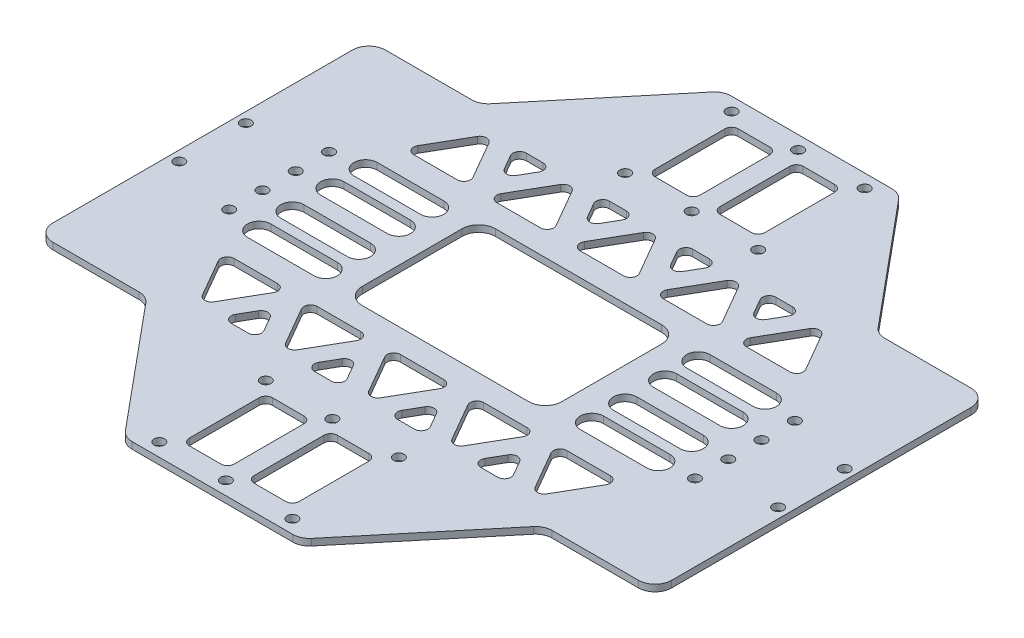
SolidWorks part; units mm, degrees
material "Hexcel AS4C (3000 丝)"
ref_plane "前视基准面" through (0, 0, 0) normal (0, 0, 1) x (1, 0, 0)
ref_plane "上视基准面" through (0, 0, 0) normal (0, 1, 0) x (1, 0, 0)
ref_plane "右视基准面" through (0, 0, 0) normal (1, 0, 0) x (0, 0, -1)
sketch "草图1" plane through (0, 0, 0) normal (0, 1, 0) x (1, 0, 0)
  line L0 (-90, 50) -> (-90, -50) construction
  line L1 (-93, 50) -> (93, 50)
  line L2 (-93, 50) -> (-93, -50)
  line L3 (-93, -50) -> (93, -50)
  line L4 (93, 50) -> (93, -50)
  line L5 (0, -50) -> (0, 50) construction
  line L6 (-93, 0) -> (93, 0) construction
  circle A0 centre (-90, 10) radius 1.6
  circle A1 centre (-90, -10) radius 1.6
  circle A2 centre (90, -10) radius 1.6
  circle A3 centre (90, 10) radius 1.6
  point P0 (0, 0)
  dimension "D3" = 3.2
  dimension "D1" = 100
  dimension "187" = 186
  dimension "D2" = 3
  dimension "D4" = 10
extrude "凸台-拉伸1" add sketch "草图1" along normal blind 2
sketch "草图2" plane through (0, 0, 0) normal (0, -1, 0) x (1, 0, 0)
  line L0 (0, 50) -> (0, -49950) construction
  line L1 (-93, 50) -> (93, 50) construction
  line L2 (-93.5, 0) -> (49906.5, 0) construction
  line L3 (-26.5, 50) -> (26.5, 50)
  line L4 (-26.5, 50) -> (-26.5, 90)
  line L5 (-26.5, 90) -> (26.5, 90)
  line L6 (26.5, 50) -> (26.5, 90)
  line L7 (0, 90) -> (0, 50) construction
  line L8 (-26.5, 70) -> (26.5, 70) construction
  line L9 (-93, -50) -> (-93, 50) construction
  line L10 (-26.5, -90) -> (26.5, -90)
  line L11 (26.5, -50) -> (26.5, -90)
  line L12 (-26.5, -50) -> (26.5, -50)
  line L13 (-26.5, -50) -> (-26.5, -90)
  line L14 (-20, 54) -> (20, 54) construction
  line L15 (-20, 86) -> (20, 86) construction
  line L16 (-20, 86) -> (-20, 54) construction
  line L17 (-20, 54) -> (20, 54) construction
  line L18 (20, 86) -> (20, 54) construction
  line L19 (0, 54) -> (0, 86) construction
  line L20 (-20, 70) -> (20, 70) construction
  line L21 (-20, -70) -> (20, -70) construction
  line L22 (0, -54) -> (0, -86) construction
  line L23 (20, -86) -> (20, -54) construction
  line L24 (-20, -54) -> (20, -54) construction
  line L25 (-20, -86) -> (-20, -54) construction
  line L26 (-20, -86) -> (20, -86) construction
  line L27 (-20, -54) -> (20, -54) construction
  line L28 (-26.5, -70) -> (26.5, -70) construction
  circle A0 centre (-20, 86) radius 1.6
  circle A1 centre (0, 86) radius 1.6
  circle A2 centre (20, 86) radius 1.6
  circle A3 centre (20, 54) radius 1.6
  circle A4 centre (0, 54) radius 1.6
  circle A5 centre (-20, 54) radius 1.6
  circle A6 centre (-20, -54) radius 1.6
  circle A7 centre (0, -54) radius 1.6
  circle A8 centre (20, -54) radius 1.6
  circle A9 centre (20, -86) radius 1.6
  circle A10 centre (0, -86) radius 1.6
  circle A11 centre (-20, -86) radius 1.6
  point P4 (0, 50)
  point P13 (-93, 0)
  point P18 (0, 70)
  point P44 (0, -70)
  point P81 (0, 70)
  dimension "D4" = 3.2
  dimension "D1" = 40
  dimension "D2" = 32
  dimension "50" = 53
  dimension "D3" = 40
extrude "凸台-拉伸2" add sketch "草图2" against normal up to surface (2 mm away) up to face at (90, 2, 8.4)
sketch "草图3" plane through (0, 2, 0) normal (0, 1, 0) x (1, 0, 0)
  line L0 (0, 90) -> (0, -49910) construction
  line L1 (-26.5, 90) -> (26.5, 90) construction
  line L2 (-93.5, 0) -> (49906.5, 0) construction
  line L3 (-93, 50) -> (-93, -50) construction
  line L4 (-70, 50) -> (-70, -50) construction
  line L5 (-26.5, 50) -> (-93, 50) construction
  line L6 (-93, -50) -> (-26.5, -50) construction
  line L7 (-70, -15) -> (-70, -5) construction
  line L8 (70, -15) -> (70, -5) construction
  circle A0 centre (-70, -15) radius 1.6
  circle A1 centre (-70, -5) radius 1.6
  circle A2 centre (-70, 5) radius 1.6
  circle A3 centre (-70, 15) radius 1.6
  circle A4 centre (70, 15) radius 1.6
  circle A5 centre (70, 5) radius 1.6
  circle A6 centre (70, -5) radius 1.6
  circle A7 centre (70, -15) radius 1.6
  point P4 (0, 90)
  point P9 (-93, 0)
  dimension "D1" = 3.2
  dimension "D3" = 10
  dimension "D4" = 15
  dimension "D5" = 70
  dimension "D2" = 4
extrude "切除-拉伸1" cut sketch "草图3" against normal through all
sketch "草图4" plane through (0, 2, 0) normal (0, 1, 0) x (1, 0, 0)
  line L0 (-26.5, 90) -> (-59.75, 50)
  line L1 (-26.5, 50) -> (-93, 50) construction
  line L2 (-59.75, 50) -> (-26.5, 50)
  line L3 (-26.5, 50) -> (-26.5, 90)
  line L4 (0, 90) -> (0, -49910) construction
  line L5 (-26.5, 90) -> (26.5, 90) construction
  line L6 (-93.5, 0) -> (-50093.5, 0) construction
  line L7 (-93, 50) -> (-93, -50) construction
  line L8 (59.75, 50) -> (26.5, 50)
  line L9 (26.5, 90) -> (59.75, 50)
  line L10 (26.5, 50) -> (26.5, 90)
  line L11 (26.5, -90) -> (59.75, -50)
  line L12 (26.5, -50) -> (26.5, -90)
  line L13 (59.75, -50) -> (26.5, -50)
  line L14 (-59.75, -50) -> (-26.5, -50)
  line L15 (-26.5, -90) -> (-59.75, -50)
  line L16 (-26.5, -50) -> (-26.5, -90)
  point P11 (0, 90)
  point P16 (-93, 0)
extrude "凸台-拉伸3" add sketch "草图4" against normal up to surface (2 mm away) up to face at (-70, 0, 6.6)
sketch "草图5" plane through (0, 0, 0) normal (0, -1, 0) x (1, 0, 0)
  line L0 (-93.5, 0) -> (-50093.5, 0) construction
  line L1 (-93, -50) -> (-93, 50) construction
  line L2 (16.5, 57.5) -> (3, 57.5)
  line L3 (-16.5, 82.5) -> (-3, 82.5)
  line L4 (-20, 86) -> (20, 86) construction
  line L5 (-20, 86) -> (-20, 54) construction
  line L6 (-20, 54) -> (20, 54) construction
  line L7 (20, 86) -> (20, 54) construction
  line L8 (0, 54) -> (0, 86) construction
  line L9 (-20, 70) -> (20, 70) construction
  line L10 (-16.5, 82.5) -> (-16.5, 57.5)
  line L11 (-16.5, 57.5) -> (-3, 57.5)
  line L12 (-3, 82.5) -> (-3, 57.5)
  line L13 (-9.75, 57.5) -> (-9.75, 82.5) construction
  line L14 (-16.5, 70) -> (-3, 70) construction
  line L15 (3, 82.5) -> (3, 57.5)
  line L16 (16.5, 82.5) -> (3, 82.5)
  line L17 (16.5, 82.5) -> (16.5, 57.5)
  line L18 (16.5, -82.5) -> (16.5, -57.5)
  line L19 (16.5, -82.5) -> (3, -82.5)
  line L20 (3, -82.5) -> (3, -57.5)
  line L21 (16.5, -57.5) -> (3, -57.5)
  line L22 (-16.5, -57.5) -> (-3, -57.5)
  line L23 (-3, -82.5) -> (-3, -57.5)
  line L24 (-16.5, -82.5) -> (-3, -82.5)
  line L25 (-16.5, -82.5) -> (-16.5, -57.5)
  line L26 (-60, -6) -> (-40, -6) construction
  line L27 (-60, -2.5) -> (-40, -2.5)
  line L28 (-30, 20) -> (30, 20)
  line L29 (-30, 20) -> (-30, -20)
  line L30 (-30, -20) -> (30, -20)
  line L31 (30, 20) -> (30, -20)
  line L32 (0, -20) -> (0, 20) construction
  line L33 (-30, 0) -> (30, 0) construction
  line L34 (-60, -9.5) -> (-40, -9.5)
  line L35 (-70, -5) -> (-30, -5) construction
  line L36 (-50, -5) -> (-50, -50005) construction
  line L37 (-60, -19.5) -> (-40, -19.5)
  line L38 (-60, -12.5) -> (-40, -12.5)
  line L39 (-60, -16) -> (-40, -16) construction
  line L40 (-60, -9.5) -> (-60, -19.5) construction
  line L41 (-60, 16) -> (-40, 16) construction
  line L42 (-60, 12.5) -> (-40, 12.5)
  line L43 (-60, 19.5) -> (-40, 19.5)
  line L44 (-60, 6) -> (-40, 6) construction
  line L45 (-60, 2.5) -> (-40, 2.5)
  line L46 (-60, 9.5) -> (-40, 9.5)
  line L47 (60, 6) -> (40, 6) construction
  line L48 (60, 2.5) -> (40, 2.5)
  line L49 (60, 9.5) -> (40, 9.5)
  line L50 (60, 16) -> (40, 16) construction
  line L51 (60, 12.5) -> (40, 12.5)
  line L52 (60, 19.5) -> (40, 19.5)
  line L53 (60, -16) -> (40, -16) construction
  line L54 (60, -12.5) -> (40, -12.5)
  line L55 (60, -19.5) -> (40, -19.5)
  line L56 (60, -6) -> (40, -6) construction
  line L57 (60, -2.5) -> (40, -2.5)
  line L58 (60, -9.5) -> (40, -9.5)
  line L59 (0, 0) -> (0, -50000) construction
  line L60 (-50, 44.3205) -> (-60, 27)
  line L61 (-60, 27) -> (-40, 27)
  line L62 (-40, 27) -> (-50, 44.3205)
  line L63 (-15, 27) -> (-25, 44.3205)
  line L64 (-25, 44.3205) -> (-35, 27)
  line L65 (-35, 27) -> (-15, 27)
  line L66 (10, 27) -> (0, 44.3205)
  line L67 (0, 44.3205) -> (-10, 27)
  line L68 (-10, 27) -> (10, 27)
  line L69 (35, 27) -> (25, 44.3205)
  line L70 (25, 44.3205) -> (15, 27)
  line L71 (15, 27) -> (35, 27)
  line L72 (60, 27) -> (50, 44.3205)
  line L73 (50, 44.3205) -> (40, 27)
  line L74 (40, 27) -> (60, 27)
  line L75 (-40, 27) -> (-15, 27) construction
  line L76 (-43.5, 44.3205) -> (-31.5, 44.3205)
  line L77 (-31.5, 44.3205) -> (-37.5, 33.9282)
  line L78 (-37.5, 33.9282) -> (-43.5, 44.3205)
  line L79 (-50, 44.3205) -> (-25, 44.3205) construction
  line L80 (-37.5, 44.3205) -> (-37.5, -49955.6795) construction
  line L81 (-12.5, 33.9282) -> (-18.5, 44.3205)
  line L82 (-18.5, 44.3205) -> (-6.5, 44.3205)
  line L83 (-6.5, 44.3205) -> (-12.5, 33.9282)
  line L84 (12.5, 33.9282) -> (6.5, 44.3205)
  line L85 (6.5, 44.3205) -> (18.5, 44.3205)
  line L86 (18.5, 44.3205) -> (12.5, 33.9282)
  line L87 (37.5, 33.9282) -> (31.5, 44.3205)
  line L88 (31.5, 44.3205) -> (43.5, 44.3205)
  line L89 (43.5, 44.3205) -> (37.5, 33.9282)
  line L90 (-37.5, 33.9282) -> (-12.5, 33.9282) construction
  line L91 (-37.5, -33.9282) -> (-12.5, -33.9282) construction
  line L92 (-50, -44.3205) -> (-25, -44.3205) construction
  line L93 (-40, -27) -> (-15, -27) construction
  line L94 (43.5, -44.3205) -> (37.5, -33.9282)
  line L95 (31.5, -44.3205) -> (43.5, -44.3205)
  line L96 (37.5, -33.9282) -> (31.5, -44.3205)
  line L97 (18.5, -44.3205) -> (12.5, -33.9282)
  line L98 (6.5, -44.3205) -> (18.5, -44.3205)
  line L99 (12.5, -33.9282) -> (6.5, -44.3205)
  line L100 (-6.5, -44.3205) -> (-12.5, -33.9282)
  line L101 (-18.5, -44.3205) -> (-6.5, -44.3205)
  line L102 (-12.5, -33.9282) -> (-18.5, -44.3205)
  line L103 (-37.5, -33.9282) -> (-43.5, -44.3205)
  line L104 (-31.5, -44.3205) -> (-37.5, -33.9282)
  line L105 (-43.5, -44.3205) -> (-31.5, -44.3205)
  line L106 (40, -27) -> (60, -27)
  line L107 (50, -44.3205) -> (40, -27)
  line L108 (60, -27) -> (50, -44.3205)
  line L109 (15, -27) -> (35, -27)
  line L110 (25, -44.3205) -> (15, -27)
  line L111 (35, -27) -> (25, -44.3205)
  line L112 (-10, -27) -> (10, -27)
  line L113 (0, -44.3205) -> (-10, -27)
  line L114 (10, -27) -> (0, -44.3205)
  line L115 (-35, -27) -> (-15, -27)
  line L116 (-25, -44.3205) -> (-35, -27)
  line L117 (-15, -27) -> (-25, -44.3205)
  line L118 (-40, -27) -> (-50, -44.3205)
  line L119 (-60, -27) -> (-40, -27)
  line L120 (-50, -44.3205) -> (-60, -27)
  arc A0 (-60, -2.5) -> (-60, -9.5) centre (-60, -6) ccw
  arc A1 (-40, -9.5) -> (-40, -2.5) centre (-40, -6) ccw
  arc A2 (-60, -12.5) -> (-60, -19.5) centre (-60, -16) ccw
  arc A3 (-40, -19.5) -> (-40, -12.5) centre (-40, -16) ccw
  arc A4 (-60, 12.5) -> (-60, 19.5) centre (-60, 16) cw
  arc A5 (-40, 19.5) -> (-40, 12.5) centre (-40, 16) cw
  arc A6 (-60, 2.5) -> (-60, 9.5) centre (-60, 6) cw
  arc A7 (-40, 9.5) -> (-40, 2.5) centre (-40, 6) cw
  arc A8 (60, 2.5) -> (60, 9.5) centre (60, 6) ccw
  arc A9 (40, 9.5) -> (40, 2.5) centre (40, 6) ccw
  arc A10 (60, 12.5) -> (60, 19.5) centre (60, 16) ccw
  arc A11 (40, 19.5) -> (40, 12.5) centre (40, 16) ccw
  arc A12 (60, -12.5) -> (60, -19.5) centre (60, -16) cw
  arc A13 (40, -19.5) -> (40, -12.5) centre (40, -16) cw
  arc A14 (60, -2.5) -> (60, -9.5) centre (60, -6) cw
  arc A15 (40, -9.5) -> (40, -2.5) centre (40, -6) cw
  circle A16 centre (-50, 32.7735) radius 5.7735 construction
  circle A17 centre (-50, -32.7735) radius 5.7735 construction
  point P4 (-93, 0)
  point P26 (0, 0)
  point P31 (-50, -6)
  point P40 (-50, -5)
  point P44 (-50, -16)
  point P52 (-50, 16)
  point P59 (-50, 6)
  point P66 (50, 6)
  point P73 (50, 16)
  point P80 (50, -16)
  point P87 (50, -6)
  point P123 (-37.5, 44.3205)
  point P129 (-9.75, 70)
  point P158 (0, 70)
  dimension "D5" = 3.5
  dimension "D1" = 3.5
  dimension "D2" = 3.5
  dimension "D3" = 60
  dimension "3" = 3
  dimension "D4" = 40
  dimension "D6" = 20
  dimension "D7" = 6
  dimension "D9" = 10
  dimension "D10" = 20
  dimension "D11" = 5
  dimension "7" = 7
  dimension "D12" = 25
  dimension "D13" = 12
  dimension "D15" = 25
  dimension "D8" = 2
  dimension "D14" = 4
extrude "切除-拉伸2" cut sketch "草图5" against normal through all
fillet "圆角1" radius 2 70 edges at (-16.5, 1, 82.5) (-3, 1, 82.5) (-3, 1, 57.5) (-16.5, 1, 57.5) (43.5, 1, 44.3205) (37.5, 1, 33.9282) (31.5, 1, 44.3205) (-31.5, 1, -44.3205) (-43.5, 1, -44.3205) (-37.5, 1, -33.9282) (-12.5, 1, -33.9282) (-6.5, 1, -44.3205) (-18.5, 1, -44.3205) (-60, 1, -27) (-40, 1, -27) (-50, 1, -44.3205) (25, 1, 44.3205) (35, 1, 27) (15, 1, 27) (50, 1, 44.3205) (60, 1, 27) (40, 1, 27) (-6.5, 1, 44.3205) (-12.5, 1, 33.9282) (-18.5, 1, 44.3205) (18.5, 1, 44.3205) (12.5, 1, 33.9282) (6.5, 1, 44.3205) (-10, 1, -27) (10, 1, -27) (0, 1, -44.3205) (15, 1, -27) (35, 1, -27) (25, 1, -44.3205) (-25, 1, -44.3205) (-35, 1, -27) (-15, 1, -27) (31.5, 1, -44.3205) (37.5, 1, -33.9282) (43.5, 1, -44.3205) (6.5, 1, -44.3205) (12.5, 1, -33.9282) (18.5, 1, -44.3205) (40, 1, -27) (60, 1, -27) (50, 1, -44.3205) (-16.5, 1, -57.5) (-3, 1, -57.5) (-3, 1, -82.5) (-16.5, 1, -82.5) (3, 1, -82.5) (3, 1, -57.5) (16.5, 1, -57.5) (16.5, 1, -82.5) (16.5, 1, 57.5) (3, 1, 57.5) (3, 1, 82.5) (16.5, 1, 82.5) (0, 1, 44.3205) (10, 1, 27) (-10, 1, 27) (-25, 1, 44.3205) (-15, 1, 27) (-35, 1, 27) (-40, 1, 27) (-60, 1, 27) (-43.5, 1, 44.3205) (-31.5, 1, 44.3205) (-37.5, 1, 33.9282) (-50, 1, 44.3205)
fillet "圆角2" radius 5 16 edges at (-93, 1, 50) (-93, 1, -50) (-59.75, 1, -50) (-26.5, 1, -90) (26.5, 1, -90) (59.75, 1, -50) (93, 1, -50) (93, 1, 50) (59.75, 1, 50) (26.5, 1, 90) (-26.5, 1, 90) (-59.75, 1, 50) (-30, 1, 20) (30, 1, -20) (-30, 1, -20) (30, 1, 20)
sketch "草图7" plane through (0, 0, 0) normal (0, -1, 0) x (1, 0, 0)
  line L0 (0, 90) -> (0, -49910) construction
  line L1 (24.1544, 90) -> (-24.1544, 90) construction
  point P4 (0, 90)
